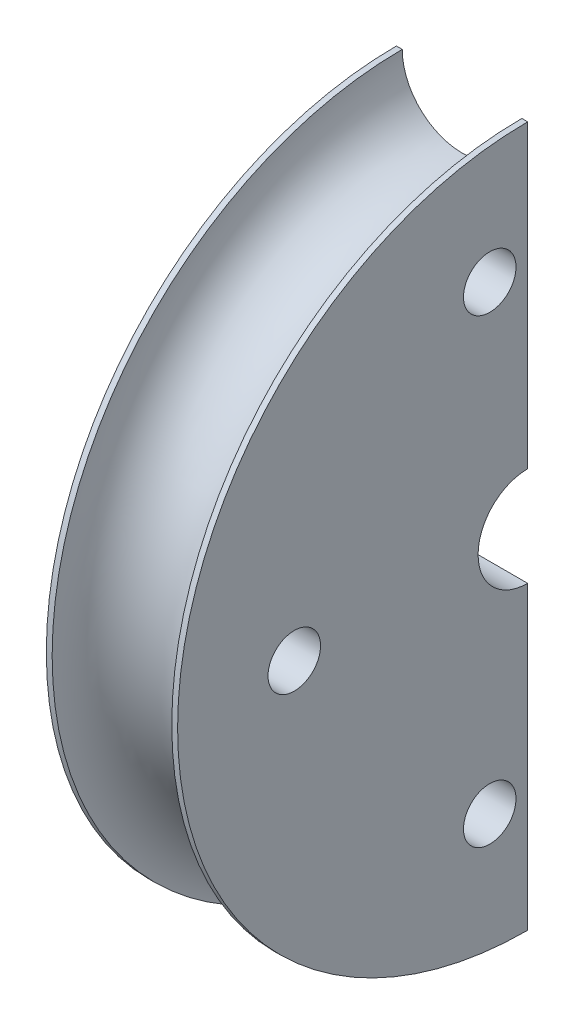
SolidWorks part; units mm, degrees
ref_plane "Plan de face" through (0, 0, 0) normal (0, 0, 1) x (1, 0, 0)
ref_plane "Plan de dessus" through (0, 0, 0) normal (0, 1, 0) x (1, 0, 0)
ref_plane "Plan de droite" through (0, 0, 0) normal (1, 0, 0) x (0, 0, -1)
sketch "Esquisse1" plane through (0, 0, 0) normal (0, 0, 1) x (1, 0, 0)
  line L0 (0, 0) -> (91.9944, 0) construction
  line L1 (0, 17) -> (0, 120)
  line L2 (45, 120) -> (45, 17)
  line L3 (0, 120) -> (2, 120)
  line L4 (43, 120) -> (45, 120)
  line L6 (0, 17) -> (45, 17)
  arc A0 (2, 120) -> (43, 120) centre (22.5, 120) ccw
  dimension "D1" = 45
  dimension "D2" = 120
  dimension "D3" = 34
  dimension "D4" = 2
  dimension "D5" = 2
revolve "Révolution1" add sketch "Esquisse1" angle 180 about L0
sketch "Esquisse2" plane through (0, 0, 0) normal (-1, 0, 0) x (0, 0, 1)
  line L0 (0, -120) -> (0, -17) construction
  line L1 (0, 120) -> (0, 17) construction
  circle A0 centre (80, 0) radius 9
  circle A1 centre (13, -78.9367) radius 9
  circle A2 centre (13, 78.9367) radius 9
  dimension "D1" = 80
  dimension "D2" = 80
  dimension "D4" = 18
  dimension "D3" = 13
  dimension "D5" = 13
  dimension "D6" = 80
extrude "Enlèv. mat.-Extru.1" cut sketch "Esquisse2" against normal through all
